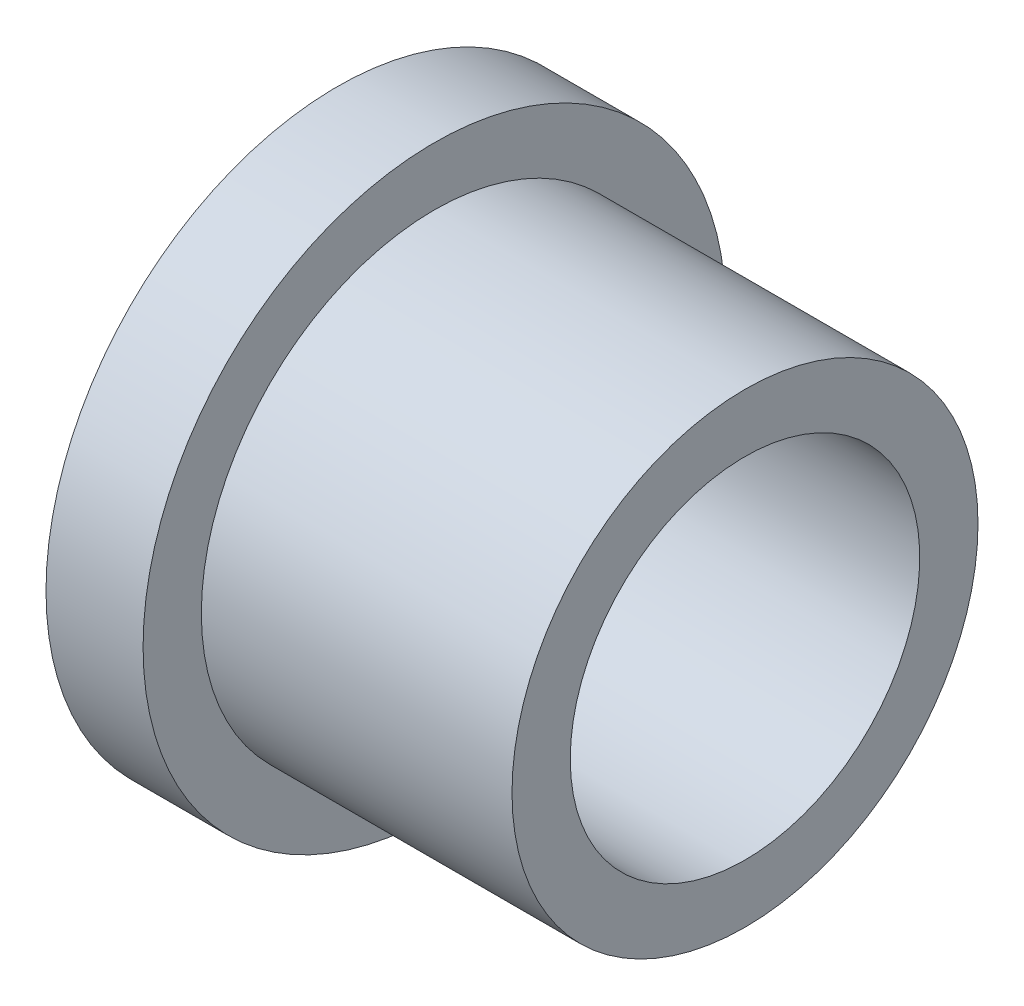
SolidWorks part; units mm, degrees
ref_plane "Front Plane" through (0, 0, 0) normal (0, 0, 1) x (1, 0, 0)
ref_plane "Top Plane" through (0, 0, 0) normal (0, 1, 0) x (1, 0, 0)
ref_plane "Right Plane" through (0, 0, 0) normal (1, 0, 0) x (0, 0, -1)
sketch "Sketch1" plane through (0, 0, 0) normal (0, 0, 1) x (1, 0, 0)
  line L0 (0, 9) -> (0, 15)
  line L1 (0, 15) -> (5, 15)
  line L2 (5, 15) -> (5, 12)
  line L3 (5, 12) -> (21, 12)
  line L4 (21, 12) -> (21, 9)
  line L5 (21, 9) -> (0, 9)
  line L6 (0, 0) -> (20.0997, 0) construction
  dimension "D1" = 30
  dimension "D2" = 24
  dimension "D3" = 3
  dimension "D4" = 16
  dimension "D5" = 21
revolve "Revolve1" add sketch "Sketch1" angle 360 about L6
